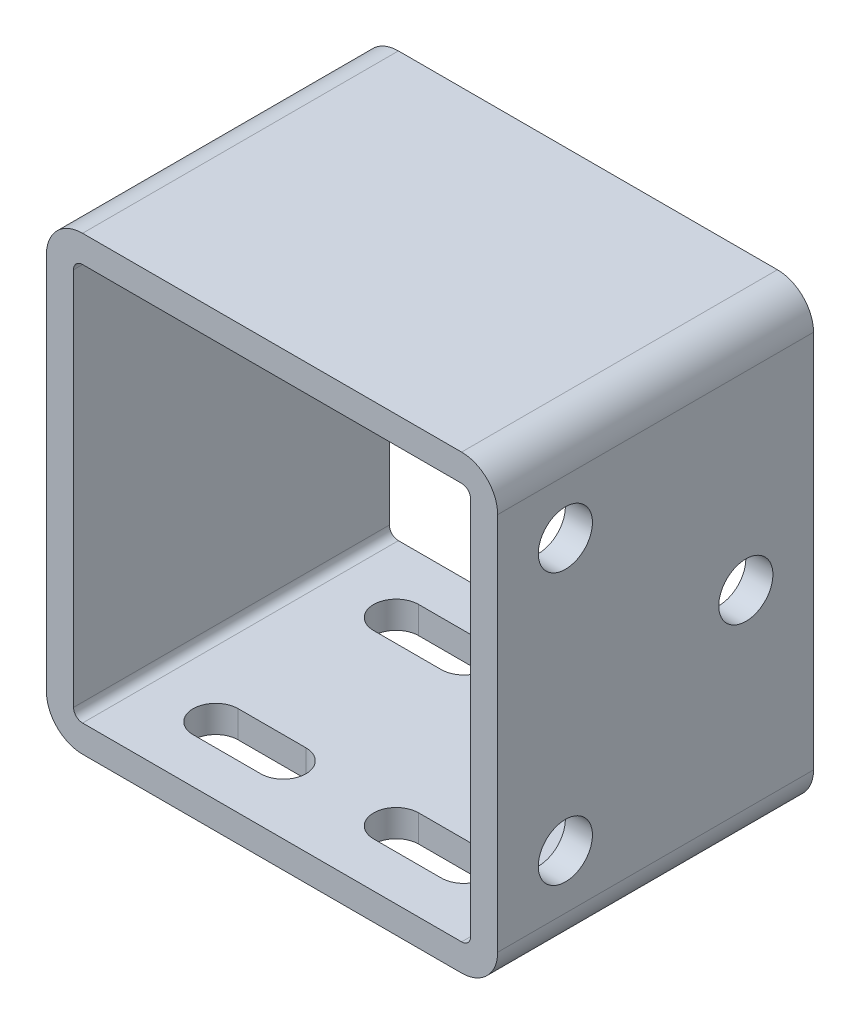
SolidWorks part; units mm, degrees
material "普通碳钢"
ref_plane "前视基准面" through (0, 0, 0) normal (0, 0, 1) x (1, 0, 0)
ref_plane "上视基准面" through (0, 0, 0) normal (0, 1, 0) x (1, 0, 0)
ref_plane "右视基准面" through (0, 0, 0) normal (1, 0, 0) x (0, 0, -1)
sketch "草图1" plane through (0, 0, 0) normal (0, 0, 1) x (1, 0, 0)
  line L0 (8, 94) -> (92, 94)
  line L1 (8, 0) -> (92, 0)
  line L2 (0, 8) -> (0, 92)
  line L3 (8, 100) -> (92, 100)
  line L4 (100, 8) -> (100, 92)
  line L9 (94, 8) -> (94, 92)
  line L10 (8, 6) -> (92, 6)
  line L11 (6, 8) -> (6, 92)
  arc A0 (8, 0) -> (0, 8) centre (8, 8) cw
  arc A1 (92, 0) -> (100, 8) centre (92, 8) ccw
  arc A2 (92, 100) -> (100, 92) centre (92, 92) cw
  arc A3 (0, 92) -> (8, 100) centre (8, 92) cw
  arc A4 (92, 94) -> (94, 92) centre (92, 92) cw
  arc A5 (92, 6) -> (94, 8) centre (92, 8) ccw
  arc A6 (8, 6) -> (6, 8) centre (8, 8) cw
  arc A7 (6, 92) -> (8, 94) centre (8, 92) cw
  point P7 (0, 0)
  point P10 (100, 0)
  point P15 (0, 100)
  dimension "D3" = 8
  dimension "D1" = 100
  dimension "D2" = 100
  dimension "D4" = 6
extrude "凸台-拉伸1" add sketch "草图1" along normal blind 70
sketch "草图2" plane through (100, 0, 0) normal (1, 0, 0) x (0, 0, -1)
  line L0 (-70, 100) -> (0, 100) construction
  line L1 (-55, 80) -> (-15, 80) construction
  line L2 (-55, 80) -> (-55, 20) construction
  line L3 (-55, 20) -> (-15, 20) construction
  line L4 (-15, 80) -> (-15, 20) construction
  line L5 (-70, 8) -> (-70, 92) construction
  circle A0 centre (-55, 80) radius 6
  circle A2 centre (-55, 20) radius 6
  circle A4 centre (-15, 50) radius 6
  dimension "D5" = 12
  dimension "D1" = 40
  dimension "D2" = 60
  dimension "D3" = 20
  dimension "D4" = 15
extrude "切除-拉伸1" cut sketch "草图2" against normal up to next
sketch "草图3" plane through (0, 0, 0) normal (0, -1, 0) x (1, 0, 0)
  line L0 (8, 70) -> (92, 70) construction
  line L1 (70, 55) -> (30, 55) construction
  line L2 (70, 55) -> (70, 15) construction
  line L3 (70, 15) -> (30, 15) construction
  line L4 (30, 55) -> (30, 15) construction
  line L5 (100, 70) -> (100, 0) construction
  line L6 (77.5, 55) -> (62.5, 55) construction
  line L7 (77.5, 60) -> (62.5, 60)
  line L10 (77.5, 50) -> (62.5, 50)
  arc A0 (62.5, 60) -> (62.5, 50) centre (62.5, 55) ccw
  arc A1 (77.5, 50) -> (77.5, 60) centre (77.5, 55) ccw
  dimension "D5" = 10
  dimension "D1" = 40
  dimension "D2" = 40
  dimension "D3" = 15
  dimension "D4" = 30
  dimension "D6" = 15
  dimension "D7" = 7.5
extrude "切除-拉伸2" cut sketch "草图3" against normal up to next (6 mm away)
pattern_linear "阵列(线性)1" count 2 spacing 40 along (0, 0, -1) count 2 spacing 40 along (-1, 0, 0) of "切除-拉伸2"
